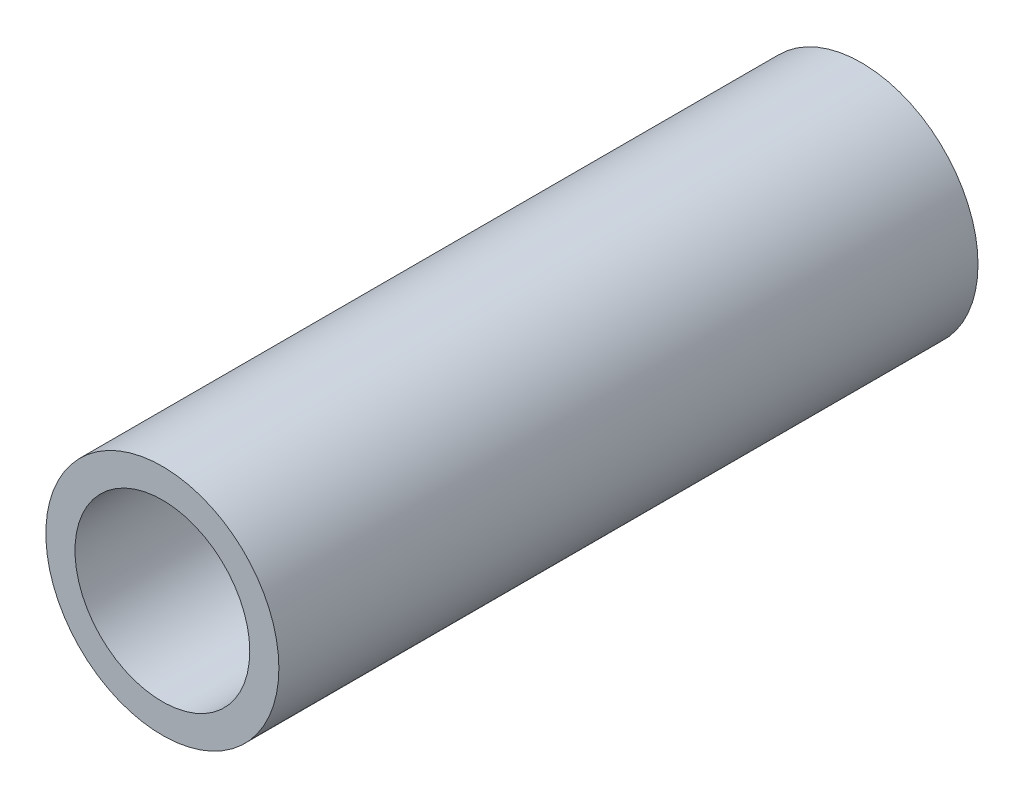
SolidWorks part; units mm, degrees
ref_plane "Alzado" through (0, 0, 0) normal (0, 0, 1) x (1, 0, 0)
ref_plane "Planta" through (0, 0, 0) normal (0, 1, 0) x (1, 0, 0)
ref_plane "Vista lateral" through (0, 0, 0) normal (1, 0, 0) x (0, 0, -1)
sketch "Croquis1" plane through (0, 0, 0) normal (0, 0, 1) x (1, 0, 0)
  circle A0 centre (0, 0) radius 20
  circle A1 centre (0, 0) radius 15
  dimension "D1" = 40
  dimension "D2" = 30
extrude "Saliente-Extruir1" add sketch "Croquis1" along normal blind 120
